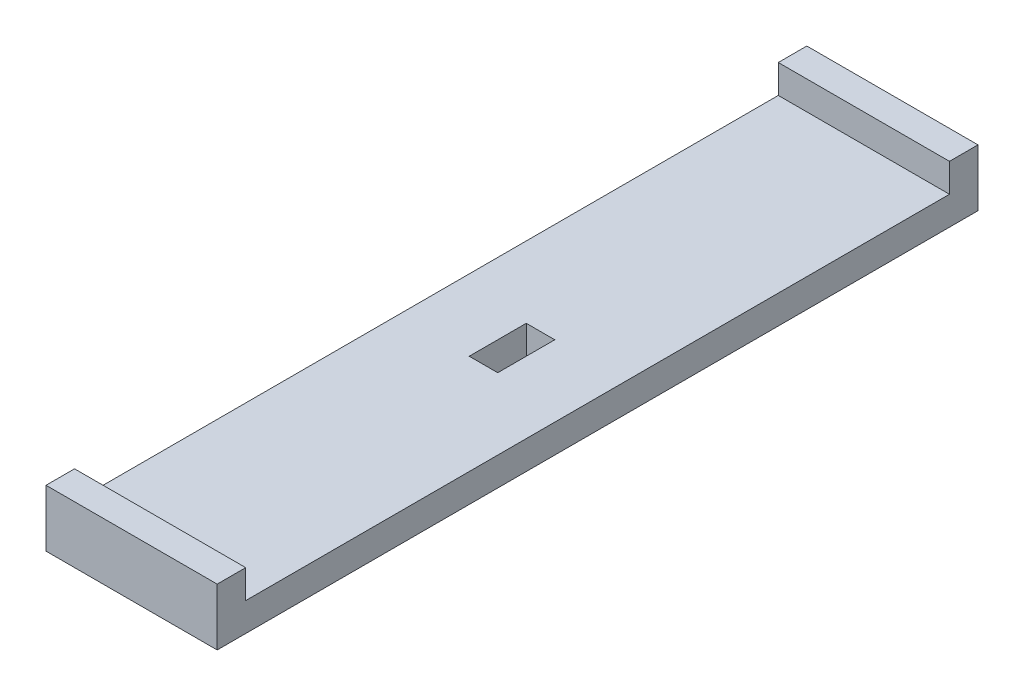
SolidWorks part; units mm, degrees
ref_plane "Front Plane" through (0, 0, 0) normal (0, 0, 1) x (1, 0, 0)
ref_plane "Top Plane" through (0, 0, 0) normal (0, 1, 0) x (1, 0, 0)
ref_plane "Right Plane" through (0, 0, 0) normal (1, 0, 0) x (0, 0, -1)
sketch "Sketch1" plane through (0, 0, 0) normal (0, 1, 0) x (1, 0, 0)
  line L1 (-1.5, -3) -> (1.5, -3)
  line L2 (-1.5, -3) -> (-1.5, 3)
  line L3 (-1.5, 3) -> (1.5, 3)
  line L4 (1.5, -3) -> (1.5, 3)
  line L5 (-1.5, -3) -> (1.5, 3) construction
  line L6 (-1.5, 3) -> (1.5, -3) construction
  line L7 (-9, -40) -> (9, -40)
  line L8 (-9, -40) -> (-9, 40)
  line L9 (-9, 40) -> (9, 40)
  line L10 (9, -40) -> (9, 40)
  line L11 (-9, -40) -> (9, 40) construction
  line L12 (-9, 40) -> (9, -40) construction
  point P0 (0, 0)
  point P6 (0, 0)
  dimension "D1" = 18
  dimension "D2" = 3
  dimension "D3" = 6
  dimension "D4" = 80
extrude "Boss-Extrude1" add sketch "Sketch1" along normal blind 3
sketch "Sketch2" plane through (0, 3, 0) normal (0, 1, 0) x (1, 0, 0)
  line L0 (-9, 40) -> (-9, -40) construction
  line L1 (9, -40) -> (-9, -40)
  line L2 (9, -40) -> (9, -37)
  line L3 (9, -37) -> (-9, -37)
  line L4 (-9, -40) -> (-9, -37)
  line L5 (9, -40) -> (9, 40) construction
  line L6 (-9, 40) -> (9, 40)
  line L7 (-9, 40) -> (-9, 37)
  line L8 (-9, 37) -> (9, 37)
  line L9 (9, 40) -> (9, 37)
  dimension "D1" = 3
extrude "Boss-Extrude2" add sketch "Sketch2" along normal blind 3
